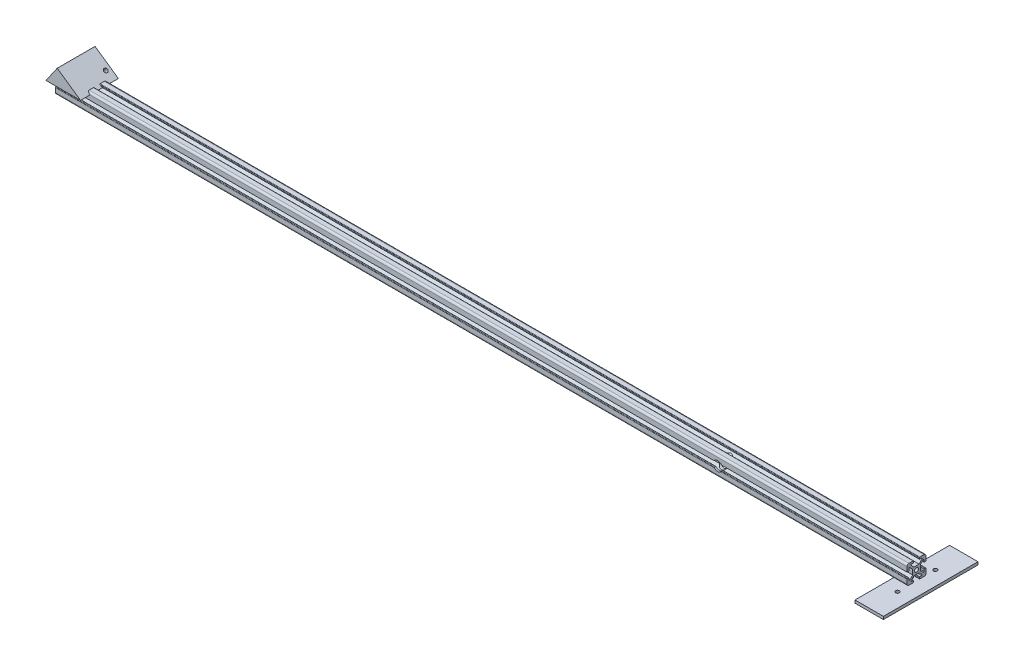
SolidWorks part; units mm, degrees
ref_plane "Front Plane" through (0, 0, 0) normal (0, 0, 1) x (1, 0, 0)
ref_plane "Top Plane" through (0, 0, 0) normal (0, 1, 0) x (1, 0, 0)
ref_plane "Right Plane" through (0, 0, 0) normal (1, 0, 0) x (0, 0, -1)
sketch "Sketch1" plane through (0, 0, 0) normal (0, 0, 1) x (1, 0, 0)
  line L0 (0, 0) -> (-1000, 0)
  point P3 (-200, 0)
  dimension "D1" = 800
  dimension "D2" = 200
other "Aluminium profile 20×20(1)"
ref_plane "Plane2" through (0, 0, 0) normal (-1, 0, 0) x (0, -1, 0)
sketch "Sketch2" plane through (0, 0, 0) normal (-1, 0, 0) x (0, -1, 0)
  line L1 (-2.6666, -4) -> (2.6666, -4)
  line L2 (-4, -2.6502) -> (-4, 2.6502)
  line L3 (-2.6666, 4) -> (2.6666, 4)
  line L4 (4, -2.6502) -> (4, 2.6502)
  line L9 (3.4986, 10) -> (7.9986, 10) construction
  line L10 (9.9986, 3.5) -> (9.9986, 8) construction
  line L11 (4, 2.6502) -> (7.1467, 5.7673)
  line L12 (2.6666, 4) -> (5.7766, 7.1486)
  line L13 (9.9986, 8) -> (9.9986, 3.5)
  line L14 (9.4986, 3) -> (8.4986, 3)
  line L15 (7.9986, 3.5) -> (7.9986, 5.4121)
  line L16 (7.9986, 10) -> (3.4986, 10)
  line L17 (2.9986, 9.5) -> (2.9986, 8.5)
  line L18 (3.4986, 8) -> (5.4209, 8)
  line L20 (-9.9986, 3.5) -> (-9.9986, 8) construction
  line L21 (-2.9986, 10) -> (-7.9986, 10) construction
  line L23 (-2.9986, 8) -> (-5.4209, 8)
  line L24 (-2.9986, 10) -> (-2.9986, 8)
  line L25 (-7.9986, 10) -> (-2.9986, 10)
  line L26 (-7.9986, 3.5) -> (-7.9986, 5.4121)
  line L27 (-9.4986, 3) -> (-8.4986, 3)
  line L28 (-9.9986, 8) -> (-9.9986, 3.5)
  line L29 (-2.6666, 4) -> (-5.7766, 7.1486)
  line L30 (-4, 2.6502) -> (-7.1467, 5.7673)
  line L32 (-3.4986, -10) -> (-7.9986, -10) construction
  line L33 (-9.9986, -3.5) -> (-9.9986, -8) construction
  line L34 (9.9986, -3.5) -> (9.9986, -8) construction
  line L35 (3.4986, -10) -> (7.9986, -10) construction
  line L37 (-4, -2.6502) -> (-7.1467, -5.7673)
  line L38 (-2.6666, -4) -> (-5.7766, -7.1486)
  line L39 (-9.9986, -8) -> (-9.9986, -3.5)
  line L40 (-9.4986, -3) -> (-8.4986, -3)
  line L41 (-7.9986, -3.5) -> (-7.9986, -5.4121)
  line L42 (-7.9986, -10) -> (-3.4986, -10)
  line L43 (-2.9986, -9.5) -> (-2.9986, -8.5)
  line L44 (-3.4986, -8) -> (-5.4209, -8)
  line L45 (3.4986, -8) -> (5.4209, -8)
  line L46 (2.9986, -9.5) -> (2.9986, -8.5)
  line L47 (7.9986, -10) -> (3.4986, -10)
  line L48 (7.9986, -3.5) -> (7.9986, -5.4121)
  line L49 (9.4986, -3) -> (8.4986, -3)
  line L50 (9.9986, -8) -> (9.9986, -3.5)
  line L51 (2.6666, -4) -> (5.7766, -7.1486)
  line L52 (4, -2.6502) -> (7.1467, -5.7673)
  circle A0 centre (0, 0) radius 2
  arc A1 (7.9986, -10) -> (9.9986, -8) centre (7.9986, -8) ccw
  arc A2 (-9.9986, -8) -> (-7.9986, -10) centre (-7.9986, -8) ccw
  arc A3 (-7.9986, 10) -> (-9.9986, 8) centre (-7.9986, 8) ccw
  arc A4 (7.9986, 10) -> (9.9986, 8) centre (7.9986, 8) cw
  arc A5 (-9.4986, -3) -> (-9.9986, -3.5) centre (-9.4986, -3.5) ccw
  arc A6 (-8.4986, -3) -> (-7.9986, -3.5) centre (-8.4986, -3.5) cw
  arc A7 (-7.1467, -5.7673) -> (-7.9986, -5.4121) centre (-7.4986, -5.4121) cw
  arc A8 (-5.7766, -7.1486) -> (-5.4209, -8) centre (-5.4209, -7.5) ccw
  arc A9 (-2.9986, -9.5) -> (-3.4986, -10) centre (-3.4986, -9.5) cw
  arc A10 (-2.9986, -8.5) -> (-3.4986, -8) centre (-3.4986, -8.5) ccw
  arc A11 (7.9986, -5.4121) -> (7.1467, -5.7673) centre (7.4986, -5.4121) cw
  arc A12 (5.4209, -8) -> (5.7766, -7.1486) centre (5.4209, -7.5) ccw
  arc A13 (3.4986, -8) -> (2.9986, -8.5) centre (3.4986, -8.5) ccw
  arc A14 (3.4986, -10) -> (2.9986, -9.5) centre (3.4986, -9.5) cw
  arc A15 (9.9986, -3.5) -> (9.4986, -3) centre (9.4986, -3.5) ccw
  arc A16 (7.9986, -3.5) -> (8.4986, -3) centre (8.4986, -3.5) cw
  arc A17 (9.9986, 3.5) -> (9.4986, 3) centre (9.4986, 3.5) cw
  arc A18 (8.4986, 3) -> (7.9986, 3.5) centre (8.4986, 3.5) cw
  arc A19 (7.9986, 5.4121) -> (7.1467, 5.7673) centre (7.4986, 5.4121) ccw
  arc A20 (3.4986, 10) -> (2.9986, 9.5) centre (3.4986, 9.5) ccw
  arc A21 (2.9986, 8.5) -> (3.4986, 8) centre (3.4986, 8.5) ccw
  arc A22 (5.4209, 8) -> (5.7766, 7.1486) centre (5.4209, 7.5) cw
  arc A23 (-5.4209, 8) -> (-5.7766, 7.1486) centre (-5.4209, 7.5) ccw
  arc A24 (-7.9986, 5.4121) -> (-7.1467, 5.7673) centre (-7.4986, 5.4121) cw
  arc A25 (-7.9986, 3.5) -> (-8.4986, 3) centre (-8.4986, 3.5) cw
  arc A26 (-9.9986, 3.5) -> (-9.4986, 3) centre (-9.4986, 3.5) ccw
  point P7 (0, 0)
  point P84 (7.9986, 3)
  point P92 (2.9986, 8)
  dimension "D1" = 4
  dimension "D2" = 2
  dimension "D3" = 0.5
sketch "Sketch3" plane through (0, 0, 10) normal (0, 0, 1) x (1, 0, 0)
  line L0 (0, 0) -> (-300, 0) construction
  circle A0 centre (-300, 0) radius 5
  dimension "D2" = 10
  dimension "D1" = 300
extrude "Cut-Extrude1" cut sketch "Sketch3" against normal blind 50 contours A0
sketch "Sketch4" plane through (0, -9.9986, 0) normal (0, -1, 0) x (1, 0, 0)
  line L0 (0, 0) -> (-100, 0) construction
  line L2 (-85, -50) -> (-115, -50)
  line L3 (-85, -50) -> (-85, 50)
  line L4 (-85, 50) -> (-115, 50)
  line L5 (-115, -50) -> (-115, 50)
  line L6 (-85, -50) -> (-115, 50) construction
  line L7 (-85, 50) -> (-115, -50) construction
  dimension "100" = 100
  dimension "D2" = 100
  dimension "D3" = 30
extrude "Boss-Extrude1" add sketch "Sketch4" along normal blind 3 separate body
sketch "Sketch5" plane through (0, -12.9986, 0) normal (0, -1, 0) x (1, 0, 0)
  line L0 (-85, 0) -> (-115, 0) construction
  line L1 (-85, -50) -> (-85, 50) construction
  line L2 (-115, 50) -> (-115, -50) construction
  line L3 (-100, 0) -> (-100, 46.3838) construction
  circle A0 centre (-100, 20) radius 2
  circle A1 centre (-100, -20) radius 2
  point P10 (-100, 0)
  dimension "D3" = 4
  dimension "D4" = 4
  dimension "D5" = 0
  dimension "D1" = 20
  dimension "D2" = 20
  dimension "D6" = 0
extrude "Cut-Extrude2" cut sketch "Sketch5" against normal blind 10
sketch "Sketch10" plane through (0, 0, 0) normal (1, 0, 0) x (0, 0, -1)
  line L1 (-26.5936, -18.5268) -> (26.5936, -18.5268)
  line L2 (-26.5936, -18.5268) -> (-26.5936, 18.5268)
  line L3 (-26.5936, 18.5268) -> (26.5936, 18.5268)
  line L4 (26.5936, -18.5268) -> (26.5936, 18.5268)
  line L5 (-26.5936, -18.5268) -> (26.5936, 18.5268) construction
  line L6 (-26.5936, 18.5268) -> (26.5936, -18.5268) construction
  point P0 (0, 0)
extrude "Cut-Extrude5" cut sketch "Sketch10" against normal blind 100
sketch "Sketch11" plane through (0, 0, 10) normal (0, 0, 1) x (1, 0, 0)
  line L0 (-1000, 7.9986) -> (-988.1448, 25.0941)
  line L1 (-988.1448, 25.0941) -> (-963.4924, 7.9986)
  line L2 (-1000, 7.9986) -> (-100, 7.9986) construction
  line L3 (-1000, 7.9986) -> (-963.4924, 7.9986)
  dimension "D1" = 30
extrude "Boss-Extrude2" add sketch "Sketch11" against normal blind 30 and the other way blind 10 separate body
sketch "Sketch13" plane through (-309.1307, -445.7776, 0) normal (0.5699, 0.8217, 0) x (0.8217, -0.5699, 0)
  line L0 (-796.3053, 0) -> (-821.3053, 0) construction
  line L1 (-796.3053, -20) -> (-796.3053, 20) construction
  circle A0 centre (-806.4152, 15) radius 2
  circle A3 centre (-806.4152, -15) radius 2
  dimension "D3" = 4
  dimension "D1" = 25
  dimension "D4" = 15
sketch "Sketch14" plane through (0, 4, 0) normal (0, 1, 0) x (1, 0, 0)
  circle A0 centre (-105.9961, 0) radius 2
  dimension "D1" = 4
extrude "Cut-Extrude8" cut sketch "Sketch14" against normal blind 40
extrude "Cut-Extrude9" cut sketch "Sketch13" against normal through all contours A0
